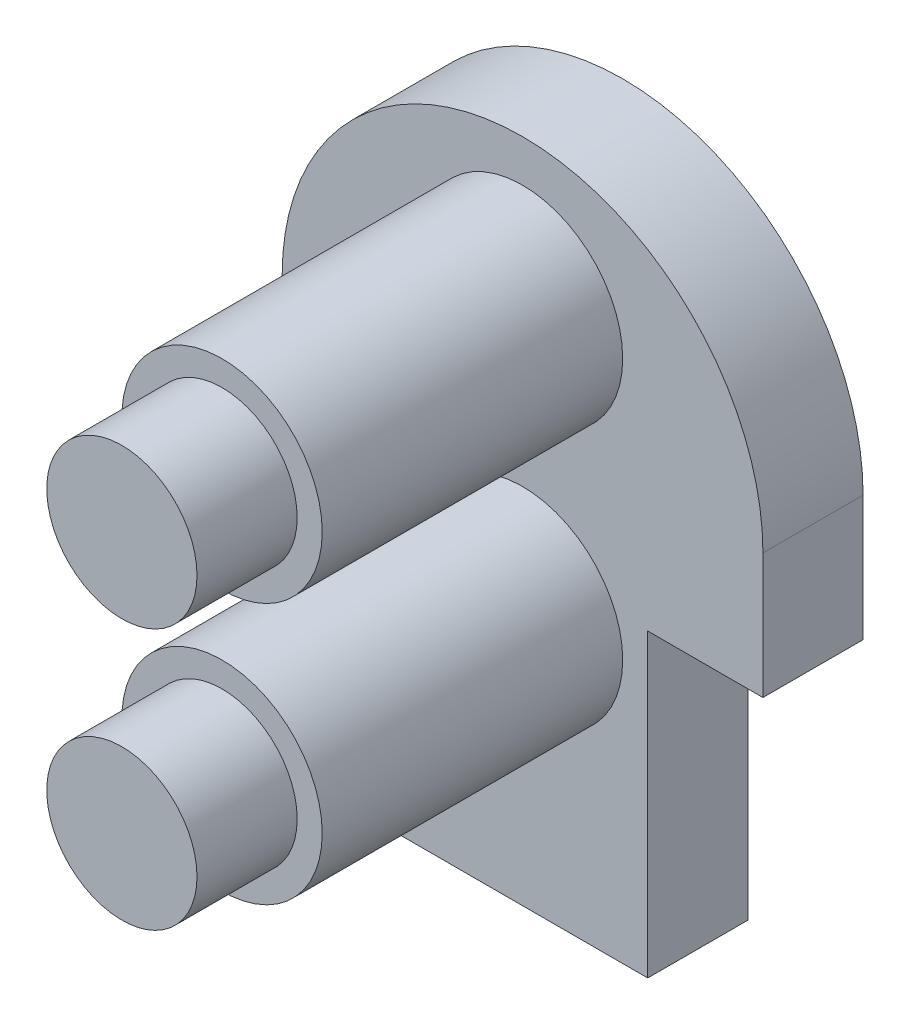
SolidWorks part; units mm, degrees
ref_plane "Front Plane" through (0, 0, 0) normal (0, 0, 1) x (1, 0, 0)
ref_plane "Top Plane" through (0, 0, 0) normal (0, 1, 0) x (1, 0, 0)
ref_plane "Right Plane" through (0, 0, 0) normal (1, 0, 0) x (0, 0, -1)
sketch "Sketch1" plane through (0, 0, 0) normal (0, 0, 1) x (1, 0, 0)
  line L0 (0, 0) -> (10, 0)
  line L1 (0, 0) -> (0, 4)
  line L2 (0, 4) -> (-2.5, 4)
  line L3 (3.3546, 18.0712) -> (6.6454, 18.0712) construction
  line L4 (-2.5, 4) -> (-2.5, 8)
  line L5 (-2.5, 8) -> (0, 8)
  line L6 (0, 8) -> (0, 12)
  line L7 (5, 0) -> (5, 27) construction
  line L8 (10, 0) -> (10, 4)
  line L9 (10, 4) -> (12.5, 4)
  line L10 (12.5, 4) -> (12.5, 8)
  line L11 (12.5, 8) -> (10, 8)
  line L12 (3.3546, 23.7712) -> (1.7091, 20.9212) construction
  line L13 (8.2909, 10.5) -> (6.6454, 13.35) construction
  line L14 (6.6454, 13.35) -> (3.3546, 13.35) construction
  line L15 (3.3546, 13.35) -> (1.7091, 10.5) construction
  line L16 (1.7091, 10.5) -> (3.3546, 7.65) construction
  line L17 (3.3546, 7.65) -> (6.6454, 7.65) construction
  line L18 (6.6454, 7.65) -> (8.2909, 10.5) construction
  line L19 (1.7091, 20.9212) -> (3.3546, 18.0712) construction
  line L20 (0, 12) -> (-4.6, 12)
  line L21 (10, 8) -> (10, 12)
  line L22 (6.6454, 18.0712) -> (8.2909, 20.9212) construction
  line L23 (8.2909, 20.9212) -> (6.6454, 23.7712) construction
  line L24 (6.6454, 23.7712) -> (3.3546, 23.7712) construction
  line L25 (10, 12) -> (14.6, 12)
  line L26 (-4.6, 12) -> (-4.6, 17)
  line L27 (14.6, 12) -> (14.6, 17)
  line L28 (3.3546, 13.35) -> (6.6454, 7.65) construction
  line L29 (6.6454, 13.35) -> (3.3546, 7.65) construction
  line L30 (3.3546, 18.0712) -> (6.6454, 23.7712) construction
  line L31 (3.3546, 23.7712) -> (6.6454, 18.0712) construction
  circle A0 centre (5, 20.9212) radius 3.2909 construction
  arc A1 (14.6, 17) -> (-4.6, 17) centre (5, 17) ccw
  circle A2 centre (5, 10.5) radius 3.2909 construction
  dimension "D5" = 2.5
  dimension "D2" = 5.7
  dimension "D8" = 4.6
  dimension "D9" = 4
  dimension "D10" = 4
  dimension "D12" = 2.5
extrude "Boss-Extrude1" add sketch "Sketch1" along normal blind 4
sketch "Sketch2" plane through (0, 0, 4) normal (0, 0, 1) x (1, 0, 0)
  line L0 (-2.5, 8) -> (0, 8)
  line L1 (0, 8) -> (0, 4)
  line L2 (0, 4) -> (-2.5, 4)
  line L3 (-2.5, 4) -> (-2.5, 8)
  line L4 (10, 8) -> (12.5, 8)
  line L5 (12.5, 8) -> (12.5, 4)
  line L6 (12.5, 4) -> (10, 4)
  line L7 (10, 4) -> (10, 8)
extrude "Cut-Extrude1" cut sketch "Sketch2" against normal up to surface (4 mm away) up to face at (5, 8.725, 0)
sketch "Sketch4" plane through (0, 0, 0) normal (0, 0, 1) x (1, 0, 0)
  circle A0 centre (5, 20.9212) radius 4
  circle A2 centre (5, 10.5) radius 4
  dimension "D3" = 8
  dimension "D1" = 10.5
  dimension "D2" = 5
  dimension "D4" = 10.4212
extrude "Boss-Extrude2" add sketch "Sketch4" along normal blind 16
sketch "Sketch5" plane through (0, 0, 16) normal (0, 0, 1) x (1, 0, 0)
  circle A0 centre (5, 10.5) radius 3
  circle A1 centre (5, 20.9212) radius 3
  dimension "D1" = 6
extrude "Boss-Extrude3" add sketch "Sketch5" along normal blind 4
equation "\"D8@Sketch1\"= 5 - \"tol2@parametersSketch@prostheticParameters.SLDPRT\""
